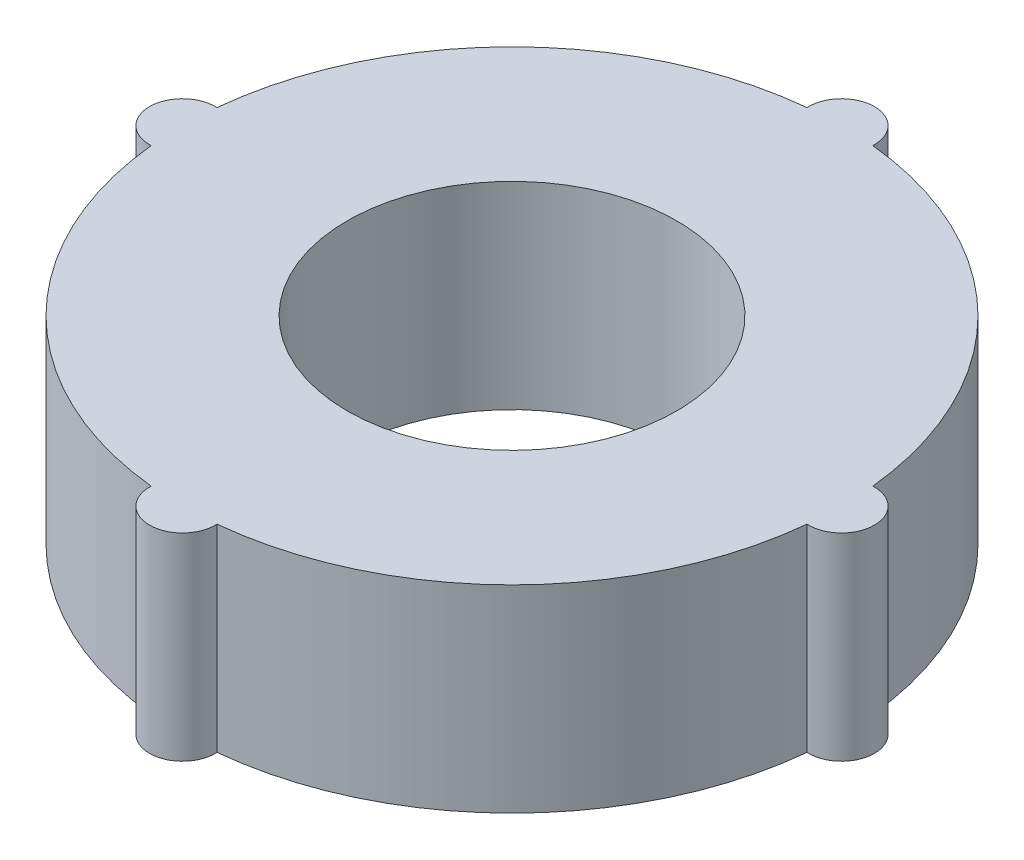
SolidWorks part; units mm, degrees
material "Acero al carbono no aleado"
ref_plane "Alzado" through (0, 0, 0) normal (0, 0, 1) x (1, 0, 0)
ref_plane "Planta" through (0, 0, 0) normal (0, 1, 0) x (1, 0, 0)
ref_plane "Vista lateral" through (0, 0, 0) normal (1, 0, 0) x (0, 0, -1)
sketch "Croquis1" plane through (0, 0, 0) normal (0, 1, 0) x (1, 0, 0)
  circle A0 centre (0, 0) radius 25
  arc A1 (-4.9937, 49.75) -> (-49.75, 4.9937) centre (0, 0) ccw
  arc A2 (4.9937, 49.75) -> (-4.9937, 49.75) centre (0, 50) ccw
  arc A3 (49.75, -4.9937) -> (49.75, 4.9937) centre (50, 0) ccw
  arc A4 (-4.9937, -49.75) -> (4.9937, -49.75) centre (0, -50) ccw
  arc A5 (-49.75, 4.9937) -> (-49.75, -4.9937) centre (-50, 0) ccw
  arc A6 (-49.75, -4.9937) -> (-4.9937, -49.75) centre (0, 0) ccw
  arc A7 (4.9937, -49.75) -> (49.75, -4.9937) centre (0, 0) ccw
  arc A8 (49.75, 4.9937) -> (4.9937, 49.75) centre (0, 0) ccw
  dimension "D1" = 50
  dimension "D2" = 100
  dimension "D3" = 10
extrude "Saliente-Extruir1" add sketch "Croquis1" along normal blind 30
